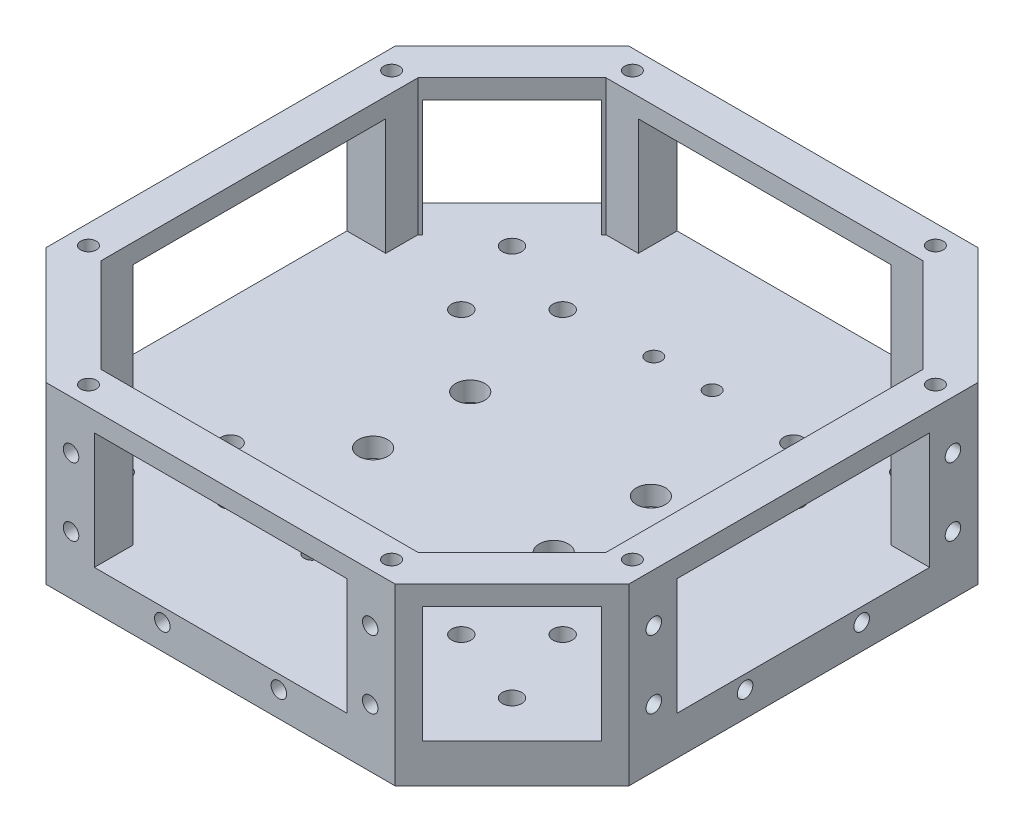
SolidWorks part; units mm, degrees
ref_plane "Front Plane" through (0, 0, 0) normal (0, 0, 1) x (1, 0, 0)
ref_plane "Top Plane" through (0, 0, 0) normal (0, 1, 0) x (1, 0, 0)
ref_plane "Right Plane" through (0, 0, 0) normal (1, 0, 0) x (0, 0, -1)
sketch "Sketch1" plane through (0, 0, 0) normal (0, 1, 0) x (1, 0, 0)
  line L20 (-150, 89.8959) -> (-89.8959, 150)
  line L21 (-89.8959, 150) -> (89.8959, 150)
  line L22 (-150, 89.8959) -> (-150, -89.8959)
  line L23 (-89.8959, -150) -> (89.8959, -150)
  line L24 (150, 89.8959) -> (150, -89.8959)
  line L25 (89.8959, 150) -> (150, 89.8959)
  line L26 (-150, -89.8959) -> (-89.8959, -150)
  line L27 (89.8959, -150) -> (150, -89.8959)
  line L28 (0, 0) -> (-267.0346, -267.0346) construction
  line L29 (0, 0) -> (-424.2751, 0) construction
  line L30 (0, 0) -> (315.5985, 315.5985) construction
  point P0 (-119.948, -119.948)
  point P4 (119.948, 119.948)
  point P12 (-150, -150)
  dimension "D1" = 300
  dimension "D2" = 300
  dimension "D3" = 150
  dimension "D4" = 150
  dimension "D5" = 85
  dimension "D6" = 85
  dimension "D7" = 45
  dimension "D8" = 150
  dimension "D9" = 150
extrude "Boss-Extrude1" add sketch "Sketch1" along normal blind 90
sketch "Sketch2" plane through (0, 90, 0) normal (0, 1, 0) x (1, 0, 0)
  line L0 (-150, 89.8959) -> (-89.8959, 150)
  line L1 (-89.8959, 150) -> (89.8959, 150)
  line L2 (89.8959, 150) -> (150, 89.8959)
  line L3 (150, 89.8959) -> (150, -89.8959)
  line L4 (150, -89.8959) -> (89.8959, -150)
  line L5 (89.8959, -150) -> (-89.8959, -150)
  line L6 (-89.8959, -150) -> (-150, -89.8959)
  line L7 (-150, -89.8959) -> (-150, 89.8959)
  line L8 (-130, -81.6117) -> (-130, 81.6117)
  line L9 (-130, 81.6117) -> (-81.6117, 130)
  line L10 (-81.6117, 130) -> (81.6117, 130)
  line L11 (81.6117, 130) -> (130, 81.6117)
  line L12 (130, 81.6117) -> (130, -81.6117)
  line L13 (130, -81.6117) -> (81.6117, -130)
  line L14 (81.6117, -130) -> (-81.6117, -130)
  line L15 (-81.6117, -130) -> (-130, -81.6117)
  dimension "D1" = 20
extrude "Cut-Extrude2" cut sketch "Sketch2" against normal blind 70 contours L9 L10 L11 L12 L13 L14 L15 L8
sketch "Sketch6" plane through (150, 0, 0) normal (1, 0, 0) x (0, 0, -1)
  line L0 (-89.8959, 0) -> (89.8959, 0) construction
  line L1 (-65, 80) -> (65, 80)
  line L2 (-65, 80) -> (-65, 20)
  line L3 (-65, 20) -> (65, 20)
  line L4 (65, 80) -> (65, 20)
  line L5 (-89.8959, 90) -> (89.8959, 90) construction
  dimension "D1" = 20
  dimension "D2" = 10
  dimension "D3" = 130
  dimension "D4" = 65
extrude "Cut-Extrude3" cut sketch "Sketch6" against normal blind 70
pattern_circular "CirPattern1" count 4 over 360 about axis through (0, 0, 0) along (0, 1, 0) of "Cut-Extrude3"
sketch "Sketch7" plane through (119.948, 0, 119.948) normal (0.7071, 0, 0.7071) x (0.7071, 0, -0.7071)
  line L0 (-42.5, 0) -> (42.5, 0) construction
  line L1 (-32.5, 80) -> (32.5, 80)
  line L2 (-32.5, 80) -> (-32.5, 20)
  line L3 (-32.5, 20) -> (32.5, 20)
  line L4 (32.5, 80) -> (32.5, 20)
  line L5 (-42.5, 90) -> (42.5, 90) construction
  point P8 (0, 90)
  dimension "D1" = 20
  dimension "D2" = 10
  dimension "D3" = 65
  dimension "D4" = 32.5
extrude "Cut-Extrude4" cut sketch "Sketch7" against normal through all
pattern_circular "CirPattern2" count 4 over 360 about axis through (0, 20, 0) along (0, -1, 0) of "Cut-Extrude4"
sketch "Sketch8" plane through (0, 20, 0) normal (0, 1, 0) x (1, 0, 0)
  line L0 (-150, 89.8959) -> (-150, -89.8959) construction
  line L1 (-89.8959, -150) -> (89.8959, -150) construction
  point P0 (-100.72, -100.72)
  point P2 (-85.48, -59.39)
  point P4 (-59.39, -85.48)
  dimension "D1" = 49.28
  dimension "D2" = 49.28
  dimension "D3" = 15.24
  dimension "D4" = 41.33
  dimension "D5" = 41.33
  dimension "D6" = 15.24
hole_wizard "Ø1.0mm Dowel Hole1" positions "Sketch8" profile "Sketch9" hole size "Ø1.0" standard "ISO" end condition through all
sketch "Sketch9" plane through (-100.72, 20, 100.72) normal (1, 0, 0) x (0, 0, 1)
  line L0 (0, 0) -> (0, 20)
  line L1 (0, 20) -> (5, 20)
  line L2 (5, 20) -> (5, 0)
  line L5 (5, 0) -> (0, 0)
  line L11 (0, -6.35) -> (0, 107.95) construction
  dimension "Thru Hole Dia." = 10
  dimension "Thru Hole Depth" = 20
sketch "Sketch10" plane through (0, 20, 0) normal (0, 1, 0) x (1, 0, 0)
  point P0 (-15.01, -88)
  dimension "D1" = 85.71
  dimension "D2" = 12.72
hole_wizard "Ø1.0mm Dowel Hole2" positions "Sketch10" profile "Sketch11" hole size "Ø1.0" standard "ISO" end condition through all
sketch "Sketch11" plane through (-15.01, 20, 88) normal (1, 0, 0) x (0, 0, 1)
  line L0 (0, 0) -> (0, 20)
  line L1 (0, 20) -> (4, 20)
  line L2 (4, 20) -> (4, 0)
  line L5 (4, 0) -> (0, 0)
  line L11 (0, -6.35) -> (0, 107.95) construction
  dimension "Thru Hole Dia." = 8
  dimension "Thru Hole Depth" = 20
mirror "Mirror1" about plane through (0, 0, 0) normal (0, 0, 1) of "Ø1.0mm Dowel Hole2", "Ø1.0mm Dowel Hole1"
mirror "Mirror2" about plane through (0, 0, 0) normal (1, 0, 0) of "Ø1.0mm Dowel Hole1", "Mirror1", "Ø1.0mm Dowel Hole2"
sketch "Sketch12" plane through (0, 20, 0) normal (0, 1, 0) x (1, 0, 0)
  point P0 (-100.72, 100.72)
sketch "Sketch14" plane through (0, 20, 0) normal (0, 1, 0) x (1, 0, 0)
  point P0 (-46.51, -25.01)
  point P2 (46.49, -25.01)
  dimension "D1" = 54.21
  dimension "D2" = 75.71
  dimension "D3" = 147.21
hole_wizard "CBORE for M5 Hex Head Bolt1" positions "Sketch14" profile "Sketch15" counterbore size "M5" standard "ISO" end condition through all
sketch "Sketch15" plane through (-46.51, 20, 25.01) normal (1, 0, 0) x (0, 0, 1)
  line L0 (0, 0) -> (0, 20)
  line L1 (0, 20) -> (4, 20)
  line L3 (4, 20) -> (4, 10)
  line L4 (4, 10) -> (7.5, 10)
  line L5 (7.5, 10) -> (7.5, 0)
  line L7 (7.5, 0) -> (0, 0)
  line L11 (0, -6.35) -> (0, 107.95) construction
  dimension "Thru Hole Dia." = 8
  dimension "Thru Hole Depth" = 20
  dimension "C'Bore Dia." = 15
  dimension "C'Bore Depth" = 10
mirror "Mirror3" about plane through (0, 0, 0) normal (0, 0, 1) of "CBORE for M5 Hex Head Bolt1"
sketch "Sketch19" plane through (0, 90, 0) normal (0, 1, 0) x (1, 0, 0)
sketch "Sketch21" plane through (0, 90, 0) normal (0, 1, 0) x (1, 0, 0)
  circle A0 centre (-100.72, -100.72) radius 5 construction
  point P0 (-140.01, -78.01)
  point P2 (-78.01, -140.01)
  point P4 (77.99, -140.01)
  point P6 (139.99, -78.01)
  dimension "D1" = 22.71
  dimension "D2" = 39.29
  dimension "D3" = 178.71
  dimension "D4" = 39.29
  dimension "D5" = 22.71
  dimension "D6" = 240.71
hole_wizard "Ø1.0mm Dowel Hole5" positions "Sketch21" profile "Sketch22" hole size "Ø1.0" standard "ISO"
sketch "Sketch22" plane through (-140.01, 90, 78.01) normal (1, 0, 0) x (0, 0, 1)
  line L0 (0, 0) -> (0, 20)
  line L2 (4, 20) -> (4, 0)
  line L3 (4, 20) -> (0, 20)
  line L4 (0, 23.4034) -> (0, 107.95) construction
  line L5 (4, 0) -> (0, 0)
  line L10 (0, 23.4034) -> (-4, 20) construction
  line L11 (0, -6.35) -> (0, 20) construction
  dimension "Hole Dia." = 8
  dimension "Hole Depth" = 20
mirror "Mirror4" about plane through (0, 0, 0) normal (0, 0, 1) of "Ø1.0mm Dowel Hole5"
sketch "Sketch23" plane through (150, 0, 0) normal (1, 0, 0) x (0, 0, -1)
  line L0 (-89.8959, 0) -> (89.8959, 0) construction
  line L1 (-89.8959, 90) -> (89.8959, 90) construction
  point P0 (-77, 65)
  point P2 (-77, 30)
  point P4 (-30, 10)
  point P6 (30, 10)
  point P8 (77, 30)
  point P10 (77, 65)
  dimension "D1" = 154
  dimension "D2" = 47
  dimension "D3" = 107
  dimension "D4" = 10
  dimension "D5" = 25
  dimension "D6" = 35
  dimension "D7" = 77
hole_wizard "Ø1.0mm Dowel Hole10" positions "Sketch27" profile "Sketch28" hole size "Ø1.0" standard "ISO"
sketch "Sketch27" plane through (150, 0, 0) normal (1, 0, 0) x (0, 0, -1)
  line L0 (-89.8959, 90) -> (89.8959, 90) construction
  point P0 (-77, 65)
  point P3 (-77, 30)
  point P6 (-30, 13)
  point P9 (30, 13)
  point P12 (77, 30)
  point P15 (77, 65)
  point P19 (0, 0)
  point P20 (0, 0)
  point P23 (0, 0)
  point P24 (0, 0)
  dimension "D1" = 77
sketch "Sketch28" plane through (150, 65, 77) normal (0, 1, 0) x (0, 0, -1)
  line L0 (0, 0) -> (0, 10)
  line L1 (0, 10) -> (4, 10)
  line L2 (4, 10) -> (4, 0)
  line L5 (4, 0) -> (0, 0)
  line L10 (0, 10) -> (-4, 10) construction
  line L11 (0, -6.35) -> (0, 107.95) construction
  dimension "Hole Dia." = 8
  dimension "Hole Depth" = 10
  dimension "Drill Angle" = 180
mirror "Mirror5" about plane through (0, 0, 0) normal (1, 0, 0) of "Ø1.0mm Dowel Hole10"
sketch "Sketch29" plane through (0, 0, 150) normal (0, 0, 1) x (1, 0, 0)
sketch "Sketch31" plane through (0, 0, 150) normal (0, 0, 1) x (1, 0, 0)
  line L0 (-89.8959, 90) -> (89.8959, 90) construction
  point P0 (-77, 65)
  point P2 (-77, 30)
  point P4 (-30, 13)
  point P6 (30, 13)
  point P8 (77, 30)
  point P10 (77, 65)
  dimension "D1" = 25
  dimension "D2" = 35
  dimension "D3" = 47
  dimension "D4" = 107
  dimension "D5" = 154
  dimension "D6" = 77
  dimension "D7" = 77
hole_wizard "Ø1.0mm Dowel Hole11" positions "Sketch31" profile "Sketch30" hole size "Ø1.0" standard "ISO"
sketch "Sketch30" plane through (-77, 65, 150) normal (1, 0, 0) x (0, -1, 0)
  line L0 (0, 0) -> (0, 10)
  line L1 (0, 10) -> (4, 10)
  line L2 (4, 10) -> (4, 0)
  line L5 (4, 0) -> (0, 0)
  line L10 (0, 10) -> (-4, 10) construction
  line L11 (0, -6.35) -> (0, 107.95) construction
  dimension "Hole Dia." = 8
  dimension "Hole Depth" = 10
  dimension "Drill Angle" = 180
mirror "Mirror6" about plane through (0, 0, 0) normal (0, 0, 1) of "Ø1.0mm Dowel Hole11"
